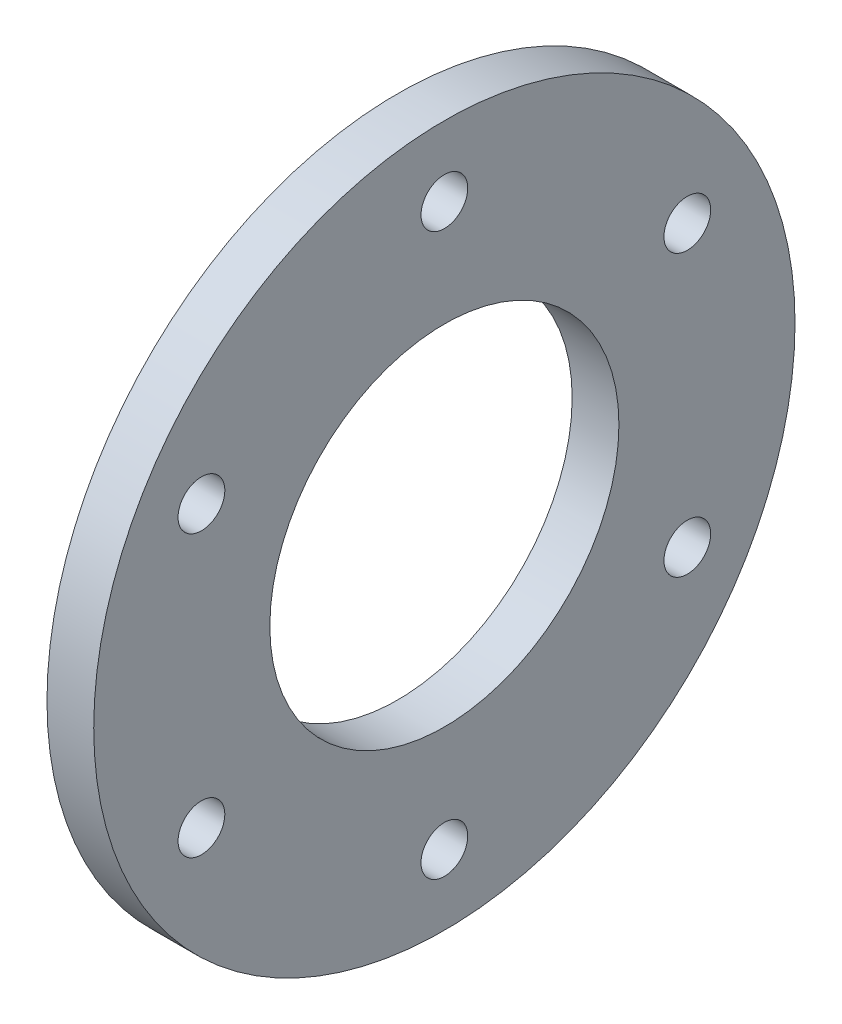
SolidWorks part; units mm, degrees
ref_plane "Front Plane" through (0, 0, 0) normal (0, 0, 1) x (1, 0, 0)
ref_plane "Top Plane" through (0, 0, 0) normal (0, 1, 0) x (1, 0, 0)
ref_plane "Right Plane" through (0, 0, 0) normal (1, 0, 0) x (0, 0, -1)
sketch "Sketch1" plane through (0, 0, 0) normal (1, 0, 0) x (0, 0, -1)
  circle A0 centre (0, 0) radius 22.5
  circle A1 centre (0, 0) radius 11.2
extrude "Extrude1" add sketch "Sketch1" along normal blind 3
sketch "Sketch2" plane through (3, 0, 0) normal (1, 0, 0) x (0, 0, -1)
  circle A0 centre (0, 0) radius 18 construction
  circle A1 centre (0, 18) radius 1.5
extrude "Cut-Extrude1" cut sketch "Sketch2" against normal through all
pattern_circular "CirPattern1" count 6 over 360 about axis through (0, 0, 0) along (1, 0, 0) of "Cut-Extrude1"
